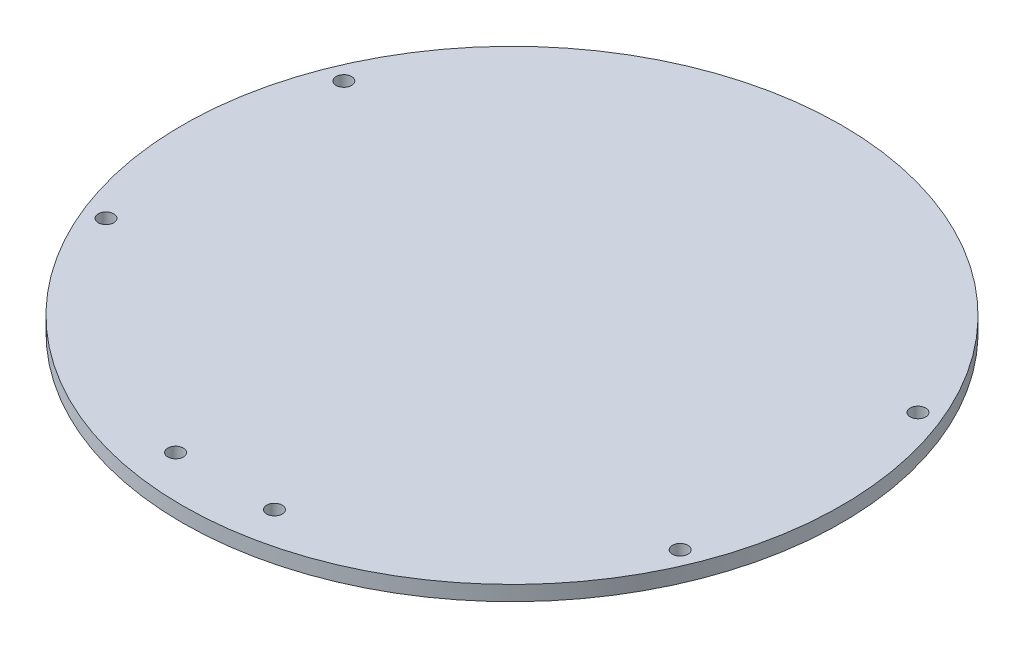
SolidWorks part; units mm, degrees
ref_plane "Front Plane" through (0, 0, 0) normal (0, 0, 1) x (1, 0, 0)
ref_plane "Top Plane" through (0, 0, 0) normal (0, 1, 0) x (1, 0, 0)
ref_plane "Right Plane" through (0, 0, 0) normal (1, 0, 0) x (0, 0, -1)
sketch "Base w/ Motor Mounts" plane through (0, 0, 0) normal (0, 1, 0) x (1, 0, 0)
  line L0 (0, 70) -> (0, -70) construction
  line L1 (0, 0) -> (70, 0) construction
  circle A0 centre (0, 0) radius 70
  dimension "D6" = 140
sketch "Standoffs (top / bottom)" plane through (0, 0, 0) normal (0, 1, 0) x (1, 0, 0)
  line L0 (0, 0) -> (64.6716, 26.7878) construction
  line L1 (0, 0) -> (49.4975, 49.4975) construction
  line L2 (0, 0) -> (26.7878, 64.6716) construction
  line L3 (0, 0) -> (70, 0) construction
  line L4 (-70, 0) -> (70, 0) construction
  line L5 (0, 0) -> (64.6716, -26.7878) construction
  line L6 (0, 0) -> (49.4975, -49.4975) construction
  line L7 (0, 0) -> (26.7878, -64.6716) construction
  line L8 (0, 70) -> (0, -70) construction
  line L9 (0, 0) -> (-26.7878, -64.6716) construction
  line L10 (0, 0) -> (-49.4975, -49.4975) construction
  line L11 (0, 0) -> (-64.6716, -26.7878) construction
  line L12 (0, 0) -> (-26.7878, 64.6716) construction
  line L13 (0, 0) -> (-49.4975, 49.4975) construction
  line L14 (0, 0) -> (-64.6716, 26.7878) construction
  circle A0 centre (0, 0) radius 70 construction
  circle A3 centre (60.976, 25.2571) radius 1.65
  circle A6 centre (60.976, -25.2571) radius 1.65
  circle A9 centre (-60.976, -25.2571) radius 1.65
  circle A12 centre (-60.976, 25.2571) radius 1.65
  circle A14 centre (0, 0) radius 70 construction
  circle A15 centre (10.5, -60.9531) radius 1.65
  circle A16 centre (-10.5, -60.9531) radius 1.65
  dimension "D4" = 3.3
  dimension "D5" = 10.5
  dimension "D6" = 21
  dimension "D1" = 22.5
  dimension "D2" = 22.5
  dimension "D3" = 22.5
sketch "Pi and Mega Standoffs" plane through (0, 0, 0) normal (0, 1, 0) x (1, 0, 0)
  line L0 (0, 70) -> (0, -70) construction
  line L1 (-38.1, 55) -> (19.9, 55) construction
  line L2 (-38.1, 55) -> (-38.1, 6) construction
  line L3 (-38.1, 6) -> (19.9, 6) construction
  line L4 (19.9, 55) -> (19.9, 6) construction
  line L5 (-38.1, 55) -> (19.9, 6) construction
  line L6 (-38.1, 6) -> (19.9, 55) construction
  line L7 (0, 0) -> (70, 0) construction
  line L8 (-38.1, -6) -> (38.1, -6) construction
  line L9 (-38.1, -6) -> (-38.1, -54.2) construction
  line L10 (-38.1, -54.2) -> (38.1, -54.2) construction
  line L11 (38.1, -6) -> (38.1, -54.2) construction
  line L12 (-38.1, -6) -> (38.1, -54.2) construction
  line L13 (-38.1, -54.2) -> (38.1, -6) construction
  circle A0 centre (-38.1, 55) radius 1.4
  circle A1 centre (19.9, 55) radius 1.4
  circle A2 centre (19.9, 6) radius 1.4
  circle A3 centre (-38.1, 6) radius 1.4
  circle A4 centre (-38.1, -54.2) radius 1.65
  circle A5 centre (-36.8, -6) radius 1.65
  circle A6 centre (38.1, -6) radius 1.65
  point P0 (-10.6204, 31.3097)
  point P11 (0, -30.1)
  dimension "D3" = 2.8
  dimension "D5" = 3.3
  dimension "D1" = 49
  dimension "D2" = 58
  dimension "D4" = 76.2
  dimension "D6" = 1.3
  dimension "D7" = 74.9
  dimension "D8" = 48.2
  dimension "D9" = 6
  dimension "D10" = 6
extrude "Boss-Extrude1" add sketch "Base w/ Motor Mounts" along normal blind 3.175
extrude "Cut-Extrude2" cut sketch "Standoffs (top / bottom)" along normal blind 3.175
equation "\"D10@Pi and Mega Standoffs\"=\"D9@Pi and Mega Standoffs\""
